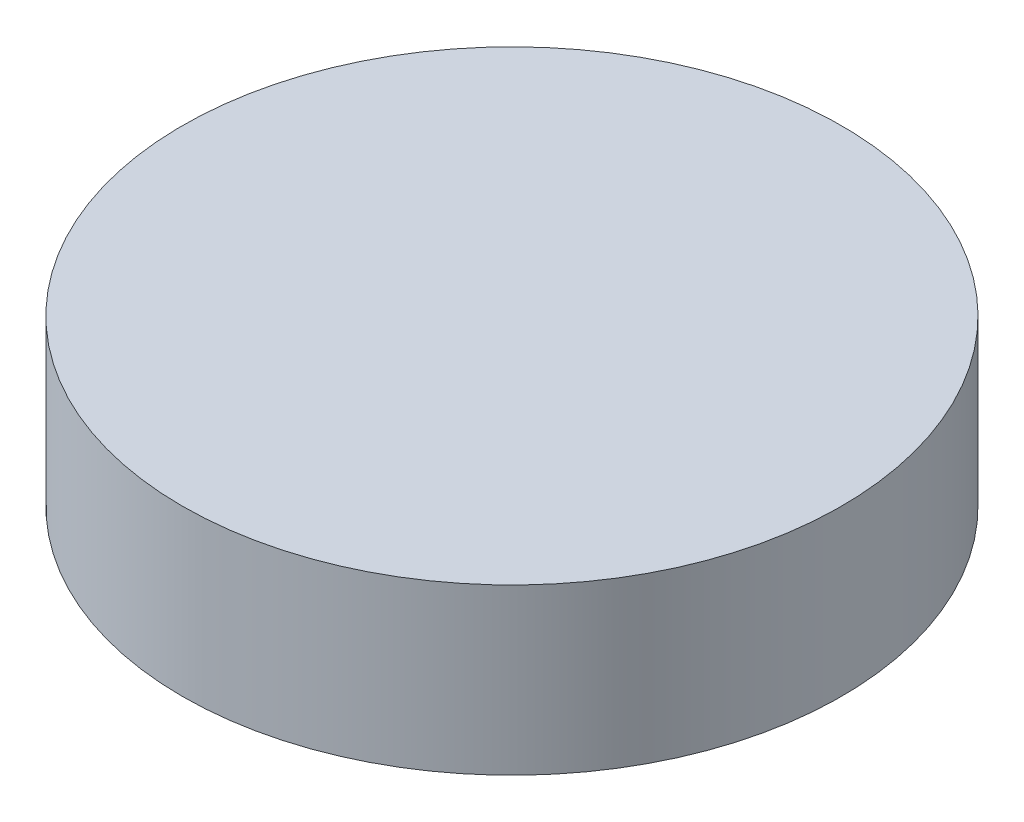
SolidWorks part; units mm, degrees
material "PE Low Density Film"
ref_plane "Front Plane" through (0, 0, 0) normal (0, 0, 1) x (1, 0, 0)
ref_plane "Top Plane" through (0, 0, 0) normal (0, 1, 0) x (1, 0, 0)
ref_plane "Right Plane" through (0, 0, 0) normal (1, 0, 0) x (0, 0, -1)
sketch "Sketch1" plane through (0, 0, 0) normal (0, 1, 0) x (1, 0, 0)
  circle A1 centre (0, 0) radius 20
extrude "Boss-Extrude1" add sketch "Sketch1" along normal blind 10
sketch "Sketch2" plane through (0, 0, 0) normal (0, 1, 0) x (1, 0, 0)
  circle A0 centre (0, 0) radius 5
extrude "Cut-Extrude1" cut sketch "Sketch2" along normal blind 5
